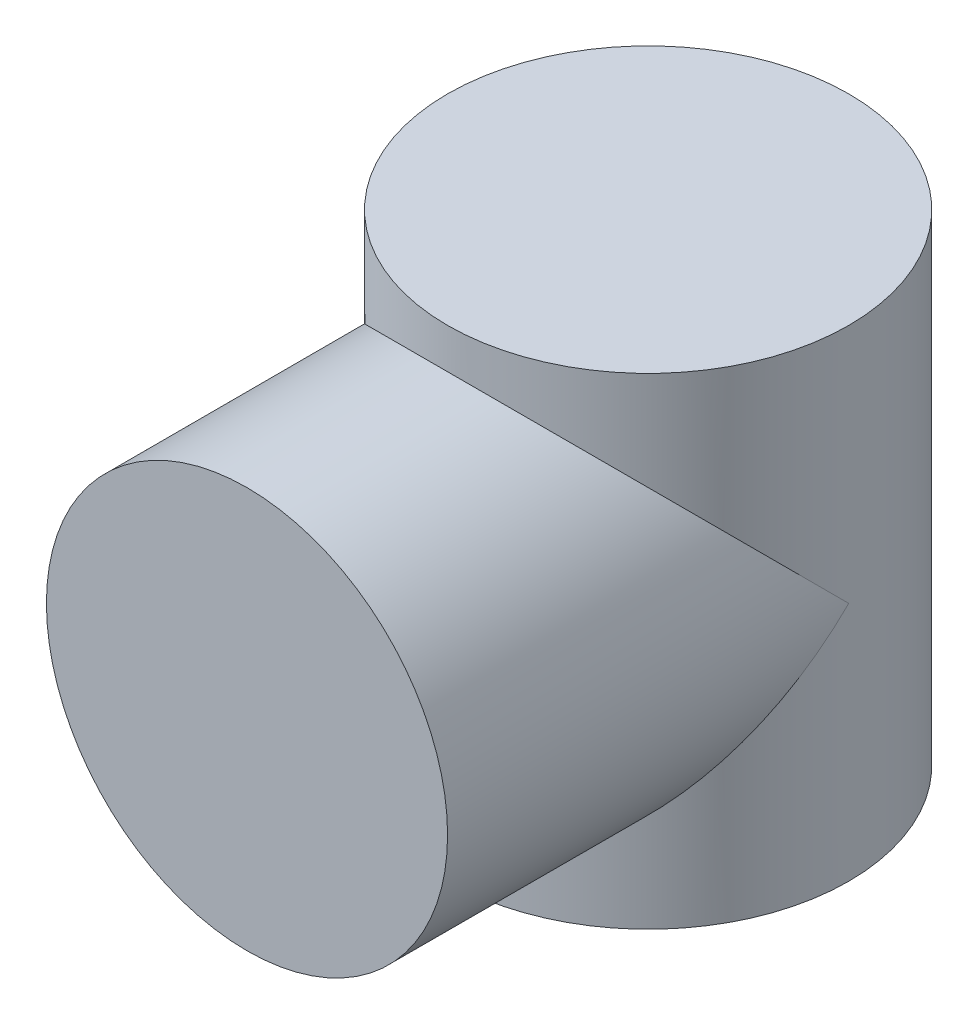
SolidWorks part; units mm, degrees
ref_plane "前视基准面" through (0, 0, 0) normal (0, 0, 1) x (1, 0, 0)
ref_plane "上视基准面" through (0, 0, 0) normal (0, 1, 0) x (1, 0, 0)
ref_plane "右视基准面" through (0, 0, 0) normal (1, 0, 0) x (0, 0, -1)
sketch "草图1" plane through (0, 0, 0) normal (0, 1, 0) x (1, 0, 0)
  circle A0 centre (0, 0) radius 50
extrude "凸台-拉伸1" add sketch "草图1" along normal mid plane 120
sketch "草图3" plane through (0, 0, 0) normal (0, 0, 1) x (1, 0, 0)
  circle A0 centre (0, 0) radius 50
extrude "凸台-拉伸2" add sketch "草图3" along normal blind 100
